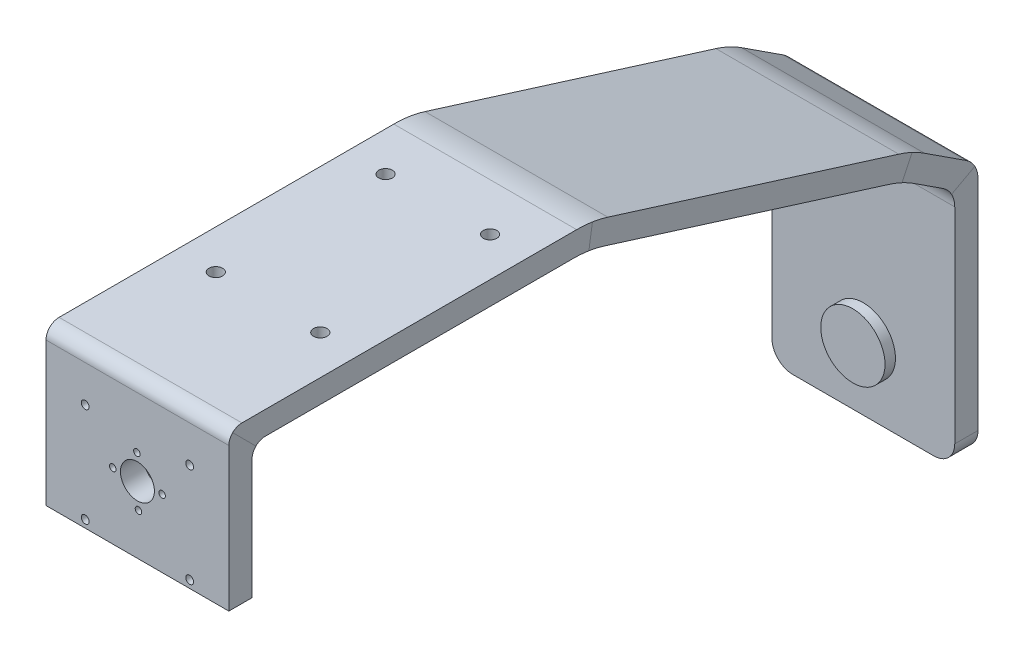
SolidWorks part; units mm, degrees
ref_plane "Front Plane" through (0, 0, 0) normal (0, 0, 1) x (1, 0, 0)
ref_plane "Top Plane" through (0, 0, 0) normal (0, 1, 0) x (1, 0, 0)
ref_plane "Right Plane" through (0, 0, 0) normal (1, 0, 0) x (0, 0, -1)
sketch "Sketch1" plane through (0, 0, 0) normal (1, 0, 0) x (0, 0, -1)
  line L0 (0, 0) -> (0, 79.9808) construction
  line L1 (0, 79.9808) -> (0, -77.9699) construction
  line L2 (0, 0) -> (-97.5268, 0) construction
  line L3 (-97.5268, 0) -> (194.488, 0) construction
  line L4 (0, 0) -> (0, 62)
  line L5 (0, 62) -> (-20, 75)
  line L6 (-140, 112.5) -> (-269, 112.5)
  line L7 (-20, 75) -> (-140, 112.5)
  line L8 (-269, 112.5) -> (-269, 61.5)
  line L9 (0, 0) -> (0, -30)
  dimension "D1" = 112.5
  dimension "D2" = 62
  dimension "D3" = 140
  dimension "D4" = 75
  dimension "D5" = 20
  dimension "D6" = 129
  dimension "D7" = 51
  dimension "D8" = 30
sketch "Sketch3" plane through (0, 0, 0) normal (0, 1, 0) x (1, 0, 0)
  line L0 (0, 0) -> (-77.6445, 0) construction
  line L1 (-77.6445, 0) -> (79.7969, 0) construction
  line L2 (0, 0) -> (0, 54.1305) construction
  line L3 (0, -97.5268) -> (0, 194.488) construction
  line L5 (35, 0) -> (-35, 0)
  line L6 (35, 0) -> (35, 8.9)
  line L7 (35, 8.9) -> (-35, 8.9)
  line L8 (-35, 0) -> (-35, 8.9)
  dimension "D1" = 8.9
  dimension "D2" = 70
sweep "Sweep1" add profiles "Sketch3" path "Sketch1"
sketch "Sketch4" plane through (0, 0, 0) normal (0, 0, 1) x (1, 0, 0)
  line L0 (0, 0) -> (63.0915, 0) construction
  line L1 (0, 0) -> (0, 15.8293) construction
  circle A1 centre (0, -5) radius 12.3
  point P3 (0, -10.8897)
  point P6 (0, -13.3171)
  dimension "D1" = 24.6
  dimension "D2" = 5
extrude "Boss-Extrude1" add sketch "Sketch4" along normal blind 4
fillet "Fillet1" radius 10 2 edges at (0, 62, 0) (0, 66.8299, -8.9)
fillet "Fillet2" radius 40 2 edges at (0, 83.1296, 16.1764) (0, 75, 20)
fillet "Fillet3" radius 8 2 edges at (-35, -30, -4.45) (35, -30, -4.45)
fillet "Fillet4" radius 40 2 edges at (0, 121.4, 138.6418) (0, 112.5, 140)
fillet "Fillet5" radius 5 2 edges at (0, 121.4, 277.9) (0, 112.5, 269)
sketch "Sketch5" plane through (0, 0, 277.9) normal (0, 0, 1) x (1, 0, 0)
  line L0 (-35, 121.4) -> (35, 121.4) construction
  line L1 (-35, 121.4) -> (35, 121.4) construction
  line L2 (0, 0) -> (0, 160.5483) construction
  line L3 (0, 87.04) -> (9.2, 87.04) construction
  circle A0 centre (0, 87.04) radius 6.5
  circle A1 centre (-0.2, 96.49) radius 1.25
  circle A2 centre (0.4, 77.59) radius 1.25
  circle A3 centre (-9.45, 86.84) radius 1.25
  circle A4 centre (9.45, 87.44) radius 1.25
  dimension "D1" = 34.36
  dimension "D2" = 13
  dimension "D3" = 2.5
  dimension "D4" = 9.45
  dimension "D5" = 9.45
  dimension "D6" = 0.2
  dimension "D7" = 0.4
  dimension "D8" = 9.45
  dimension "D9" = 9.45
  dimension "D10" = 0.4
  dimension "D11" = 0.2
extrude "Cut-Extrude1" cut sketch "Sketch5" against normal up to next
sketch "Sketch6" plane through (0, 121.4, 0) normal (0, 1, 0) x (1, 0, 0)
  line L0 (-35, -272.9) -> (35, -272.9) construction
  line L1 (-35, -272.9) -> (35, -272.9) construction
  line L2 (0, 0) -> (0, -359.3688) construction
  circle A0 centre (-20, -162.9) radius 2.6
  circle A1 centre (20, -162.9) radius 2.6
  circle A2 centre (-20, -227.9) radius 2.6
  circle A3 centre (20, -227.9) radius 2.6
  dimension "D1" = 5.2
  dimension "D3" = 110
  dimension "D4" = 45
  dimension "D5" = 20
  dimension "D2" = 20
extrude "Cut-Extrude2" cut sketch "Sketch6" against normal up to next
sketch "Sketch7" plane through (0, 0, 277.9) normal (0, 0, 1) x (1, 0, 0)
  line L0 (-35, 121.4) -> (35, 121.4) construction
  line L1 (-35, 121.4) -> (35, 121.4) construction
  line L2 (0, 0) -> (0, 196.3555) construction
  circle A0 centre (20, 102.4) radius 1.5
  circle A1 centre (20, 64.4) radius 1.5
  circle A2 centre (-20, 102.4) radius 1.5
  circle A3 centre (-20, 64.4) radius 1.5
  dimension "D1" = 3
  dimension "D2" = 20
  dimension "D3" = 20
  dimension "D4" = 19
  dimension "D5" = 38
extrude "Cut-Extrude3" cut sketch "Sketch7" against normal up to next
